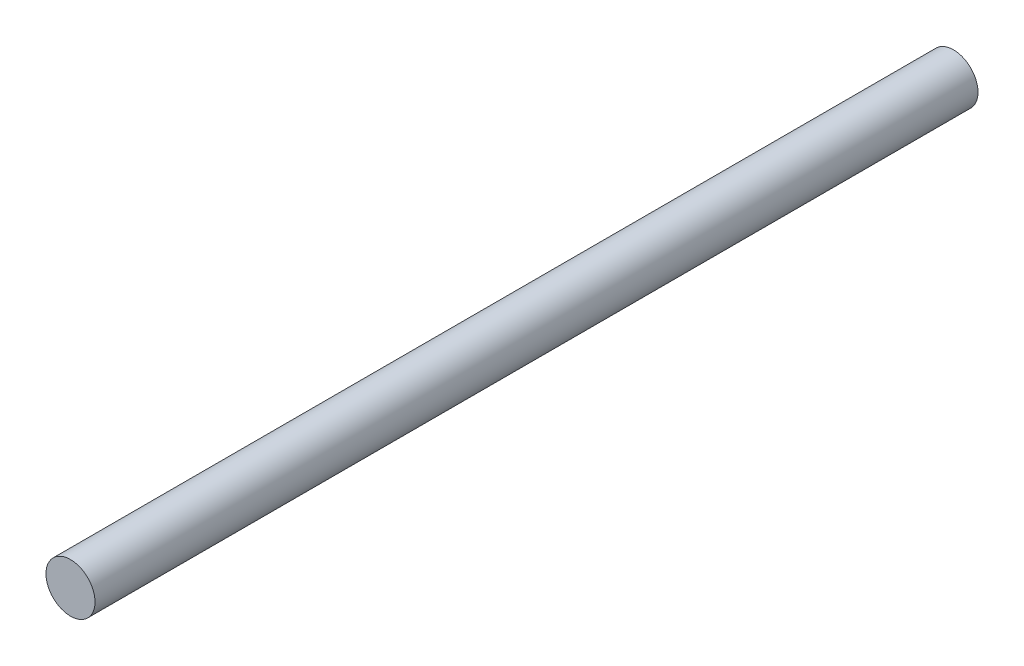
SolidWorks part; units mm, degrees
ref_plane "Ön Düzlem" through (0, 0, 0) normal (0, 0, 1) x (1, 0, 0)
ref_plane "Üst Düzlem" through (0, 0, 0) normal (0, 1, 0) x (1, 0, 0)
ref_plane "Sağ Düzlem" through (0, 0, 0) normal (1, 0, 0) x (0, 0, -1)
sketch "Çizim1" plane through (0, 0, 0) normal (0, 0, 1) x (1, 0, 0)
  circle A0 centre (0, 0) radius 5
  dimension "D1" = 10
extrude "Yükseklik-Ekstrüzyon1" add sketch "Çizim1" along normal blind 180
